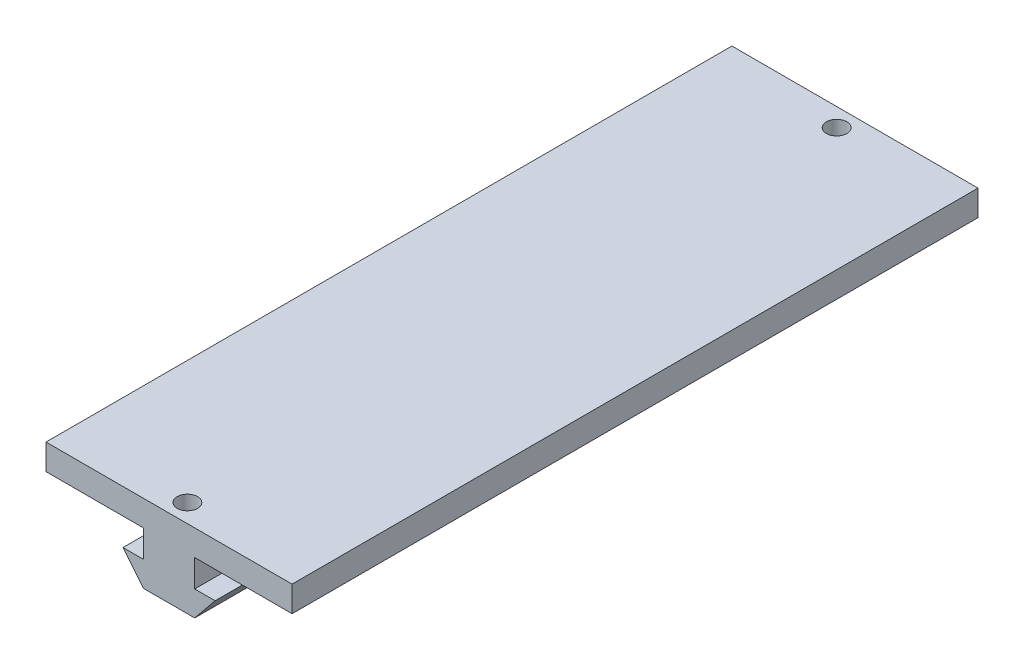
SolidWorks part; units mm, degrees
ref_plane "Front Plane" through (0, 0, 0) normal (0, 0, 1) x (1, 0, 0)
ref_plane "Top Plane" through (0, 0, 0) normal (0, 1, 0) x (1, 0, 0)
ref_plane "Right Plane" through (0, 0, 0) normal (1, 0, 0) x (0, 0, -1)
sketch "Sketch1" plane through (0, 0, 0) normal (0, 1, 0) x (1, 0, 0)
  line L1 (-23.5, -65.5) -> (23.5, -65.5)
  line L2 (-23.5, -65.5) -> (-23.5, 65.5)
  line L3 (-23.5, 65.5) -> (23.5, 65.5)
  line L4 (23.5, -65.5) -> (23.5, 65.5)
  line L5 (-23.5, -65.5) -> (23.5, 65.5) construction
  line L6 (-23.5, 65.5) -> (23.5, -65.5) construction
  point P0 (0, 0)
  dimension "D1" = 131
  dimension "D2" = 47
extrude "Boss-Extrude1" add sketch "Sketch1" along normal blind 4.9
sketch "Sketch3" plane through (0, 0, 65.5) normal (0, 0, 1) x (1, 0, 0)
  line L0 (-4.9, 0) -> (4.9, 0)
  line L1 (-23.5, 0) -> (23.5, 0) construction
  line L2 (4.9, 0) -> (4.9, -5.2)
  line L3 (4.9, -5.2) -> (8.8, -5.2)
  line L4 (8.8, -5.2) -> (4.9, -10)
  line L5 (4.9, -10) -> (-4.9, -10)
  line L6 (-4.9, -10) -> (-8.8, -5.2)
  line L7 (-8.8, -5.2) -> (-4.9, -5.2)
  line L8 (-4.9, -5.2) -> (-4.9, 0)
  line L9 (0, 4.9) -> (0, -15.5332) construction
  line L10 (-23.5, 4.9) -> (23.5, 4.9) construction
  point P5 (0, 0)
  point P16 (0, 0)
  point P17 (0, 0)
  point P18 (0, 0)
  dimension "D1" = 5.2
  dimension "D2" = 4.8
  dimension "D3" = 9.8
  dimension "D4" = 3.9
extrude "Boss-Extrude2" add sketch "Sketch3" against normal blind 50
sketch "Sketch2" plane through (0, 4.9, 0) normal (0, 1, 0) x (1, 0, 0)
  line L0 (-23.5, 0) -> (23.5, 0) construction
  line L1 (-23.5, 65.5) -> (-23.5, -65.5) construction
  line L2 (23.5, -65.5) -> (23.5, 65.5) construction
  circle A0 centre (0, 62) radius 1.95
  circle A1 centre (0, -62) radius 1.95
  point P4 (0, 0)
  dimension "D2" = 3.9
  dimension "D1" = 124
extrude "Cut-Extrude1" cut sketch "Sketch2" against normal blind 6
